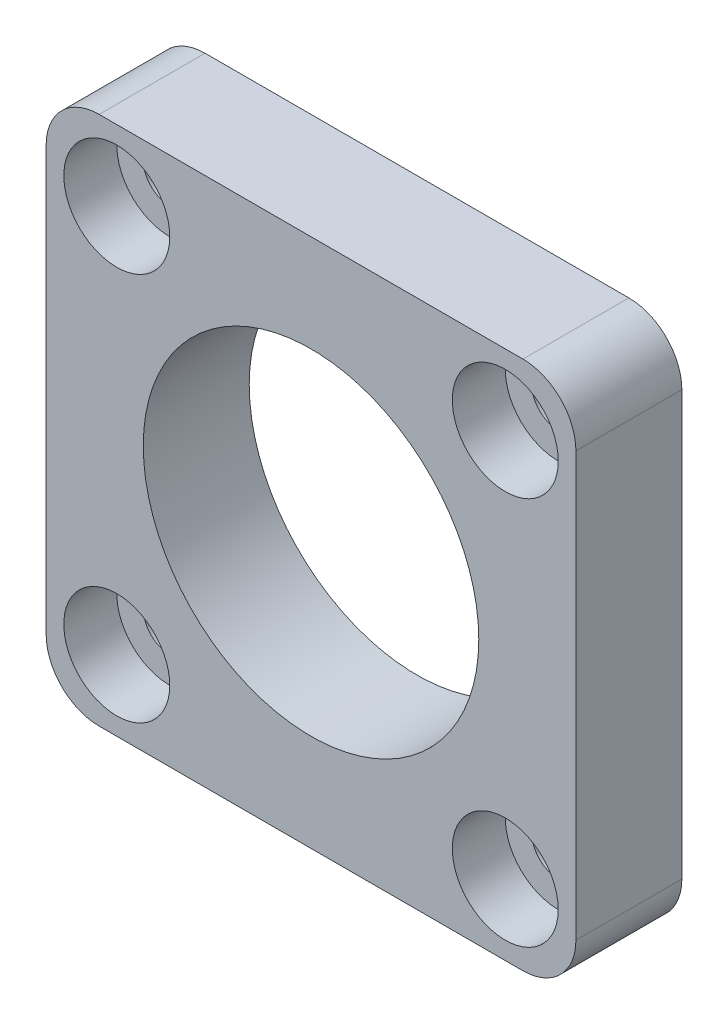
SolidWorks part; units mm, degrees
ref_plane "Front Plane" through (0, 0, 0) normal (0, 0, 1) x (1, 0, 0)
ref_plane "Top Plane" through (0, 0, 0) normal (0, 1, 0) x (1, 0, 0)
ref_plane "Right Plane" through (0, 0, 0) normal (1, 0, 0) x (0, 0, -1)
sketch "Sketch1" plane through (0, 0, 0) normal (0, 0, 1) x (1, 0, 0)
  line L1 (-15, -15) -> (15, -15)
  line L2 (-15, -15) -> (-15, 15)
  line L3 (-15, 15) -> (15, 15)
  line L4 (15, -15) -> (15, 15)
  line L5 (-15, -15) -> (15, 15) construction
  line L6 (-15, 15) -> (15, -15) construction
  circle A0 centre (0, 0) radius 9.5
  point P0 (0, 0)
  dimension "D3" = 19
  dimension "D1" = 30
  dimension "D2" = 30
extrude "Boss-Extrude1" add sketch "Sketch1" along normal blind 6
sketch "Sketch3" plane through (0, 0, 6) normal (0, 0, 1) x (1, 0, 0)
  line L1 (-11, -11) -> (11, -11) construction
  line L2 (-11, -11) -> (-11, 11) construction
  line L3 (-11, 11) -> (11, 11) construction
  line L4 (11, -11) -> (11, 11) construction
  line L5 (-11, -11) -> (11, 11) construction
  line L6 (-11, 11) -> (11, -11) construction
  circle A0 centre (-11, 11) radius 1.5
  circle A1 centre (11, 11) radius 1.5
  circle A2 centre (11, -11) radius 1.5
  circle A3 centre (-11, -11) radius 1.5
  point P0 (0, 0)
  dimension "D3" = 3
  dimension "D4" = 3
  dimension "D5" = 3
  dimension "D6" = 3
  dimension "D1" = 22
  dimension "D2" = 22
extrude "Cut-Extrude2" cut sketch "Sketch3" against normal through all
sketch "Sketch4" plane through (0, 0, 6) normal (0, 0, 1) x (1, 0, 0)
  circle A0 centre (-11, 11) radius 3
  circle A1 centre (11, 11) radius 3
  circle A2 centre (11, -11) radius 3
  circle A3 centre (-11, -11) radius 3
  dimension "D1" = 6
  dimension "D2" = 6
  dimension "D3" = 6
  dimension "D4" = 6
extrude "Cut-Extrude3" cut sketch "Sketch4" against normal blind 3
fillet "Fillet1" radius 3 4 edges at (-15, -15, 3) (15, -15, 3) (15, 15, 3) (-15, 15, 3)
